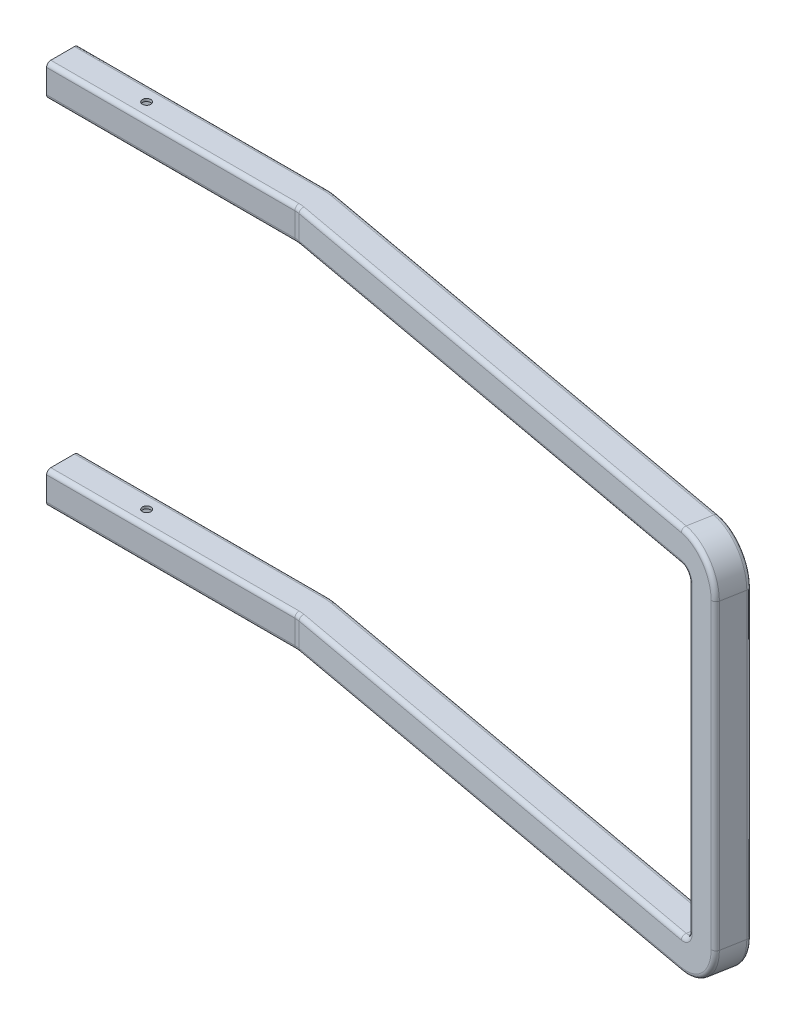
SolidWorks part; units mm, degrees
other "Markup1" [suppressed]
sketch "Sketch29" [suppressed] plane through (-50, 12.7, -12.7) normal (-0.6703, 0.7401, -0.0544) x (0.7356, 0.653, -0.1804)
sketch "Sketch30" [suppressed] plane through (-50, 20, -18.6944) normal (-0.6703, 0.7401, -0.0544) x (0.7356, 0.653, -0.1804)
sketch "Sketch34" [suppressed] plane through (-50, 20, -18.6944) normal (-0.6703, 0.7401, -0.0544) x (0.7356, 0.653, -0.1804)
sketch "Sketch35" [suppressed] plane through (-50, 30, -28.5496) normal (-0.6703, 0.7401, -0.0544) x (0.7356, 0.653, -0.1804)
sketch "Sketch36" [suppressed] plane through (-50, 30, -28.5496) normal (-0.6703, 0.7401, -0.0544) x (0.7356, 0.653, -0.1804)
sketch "Sketch37" plane through (-50, 30, -28.5496) normal (-0.6703, 0.7401, -0.0544) x (0.7356, 0.653, -0.1804)
sketch "Sketch38" plane through (-50, 25, -25) normal (-0.6703, 0.7401, -0.0544) x (0.7356, 0.653, -0.1804)
material "5052-O"
ref_plane "Front Plane" through (0, 0, 0) normal (0, 0, 1) x (1, 0, 0)
ref_plane "Top Plane" through (0, 0, 0) normal (0, 1, 0) x (1, 0, 0)
ref_plane "Right Plane" through (0, 0, 0) normal (1, 0, 0) x (0, 0, -1)
sketch "Sketch2" plane through (0, 0, 0) normal (1, 0, 0) x (0, 0, -1)
  line L1 (-14.05, -19.05) -> (14.05, -19.05)
  line L2 (-19.05, -14.05) -> (-19.05, 14.05)
  line L3 (-14.05, 19.05) -> (14.05, 19.05)
  line L4 (19.05, -14.05) -> (19.05, 14.05)
  line L5 (-19.05, -19.05) -> (19.05, 19.05) construction
  line L6 (-19.05, 19.05) -> (19.05, -19.05) construction
  arc A0 (19.05, -14.05) -> (14.05, -19.05) centre (14.05, -14.05) cw
  arc A1 (-14.05, -19.05) -> (-19.05, -14.05) centre (-14.05, -14.05) cw
  arc A2 (-19.05, 14.05) -> (-14.05, 19.05) centre (-14.05, 14.05) cw
  arc A3 (14.05, 19.05) -> (19.05, 14.05) centre (14.05, 14.05) cw
  point P0 (0, 0)
  dimension "D3" = 5
  dimension "D1" = 38.1
  dimension "D2" = 38.1
sketch3d "3DSketch2"
  line L0 (0, 0, 0) -> (840.2912, 0, 0) construction
  line L1 (840.2912, 0, 0) -> (840.2912, -210, 0) construction
  line L2 (840.2912, -210, 0) -> (840.2912, -210, 107.5) construction
  line L3 (0, 0, 0) -> (245.4843, 0, 0)
  line L4 (254.4426, 0, 0.8091) -> (810.7767, 0, 102.125)
  line L5 (0, 0, 0) -> (-50, 0, 0)
  line L6 (0, 0, 0) -> (0, -210, 0) construction
  line L7 (840.2912, -210, 107.5) -> (840.2912, -210, 287.5) construction
  line L8 (840.2912, -210, 287.5) -> (-9.7834, -210, 287.5) construction
  line L9 (840.2912, -30, 107.5) -> (840.2912, -210, 107.5)
  arc A0 (254.4426, 0, 0.8091) -> (245.4843, 0, 0) centre (245.4843, 0, 50) ccw
  arc A1 (840.2912, -30, 107.5) -> (810.7767, 0, 102.125) centre (810.7767, -30, 102.125) ccw
  point P16 (250, 0, 0)
  point P17 (245.4843, 50, 50)
  point P20 (840.2912, 0, 107.5)
  point P21 (805.4017, -30, 131.6396)
  dimension "5" = 50
  dimension "D9" = 30
  dimension "D1" = 250
  dimension "D2" = 50
  dimension "D3" = 210
  dimension "D4" = 107.5
  dimension "D5" = 210
  dimension "D6" = 600
  dimension "D7" = 180
  dimension "D8" = 210
sweep "Sweep-Thin3" add profiles "Sketch2" path "3DSketch2" parameters "D1"=3.175
sketch "Sketch21" plane through (0, 0, 0) normal (0, 1, 0) x (1, 0, 0)
  line L0 (0, 0) -> (245.4843, 0) construction
  circle A0 centre (50, 0) radius 5
  dimension "D1" = 10
  dimension "D2" = 50
extrude "Cut-Extrude3" cut sketch "Sketch21" against normal through all both and the other way through all
sketch "Sketch22" [suppressed] plane through (0, 0, 0) normal (0, 0, 1) x (1, 0, 0)
ref_plane "Plane1" [suppressed] through (0, -210, 0) normal (0, 1, 0) x (1, 0, 0)
ref_plane "Plane2" through (0, -210, 0) normal (0, -1, 0) x (-1, 0, 0)
ref_plane "Plane3" through (0, -210, 0) normal (0, -1, 0) x (-1, 0, 0)
mirror "Mirror1" about plane through (0, -210, 0) normal (0, -1, 0) of "Cut-Extrude3", "Sweep-Thin3"
ref_plane "Plane4" [suppressed] through (2.91, 0, -15.9792) normal (-0.1792, 0, 0.9838) x (0.9838, 0, 0.1792)
sketch "Sketch23" [suppressed] plane through (2.91, 0, -15.9792) normal (-0.1792, 0, 0.9838) x (0.9838, 0, 0.1792)
  line L0 (874.5043, -30) -> (874.5043, -390) construction
  line L1 (874.5043, 30) -> (674.5043, 30)
  line L2 (874.5043, 30) -> (874.5043, -450)
  line L3 (874.5043, -450) -> (674.5043, -450)
  line L4 (674.5043, 30) -> (674.5043, -450)
  line L5 (868.2597, -30) -> (868.2597, -390) construction
  point P8 (868.2597, -210)
  point P9 (874.5043, -210)
  dimension "D1" = 480
  dimension "D2" = 200
extrude "Boss-Extrude1" [suppressed] add sketch "Sketch23" along normal blind 25.4
sketch "Sketch25" [suppressed] plane through (2.91, 0, -15.9792) normal (0.1792, 0, -0.9838) x (-0.9838, 0, -0.1792)
  line L0 (-674.5043, -22.305) -> (-674.5043, -397.695) construction
  line L1 (-816.5543, -174.3) -> (-732.4543, -174.3) construction
  line L2 (-816.5543, -174.3) -> (-816.5543, -245.7) construction
  line L3 (-816.5543, -245.7) -> (-732.4543, -245.7) construction
  line L4 (-732.4543, -174.3) -> (-732.4543, -245.7) construction
  line L5 (-816.5543, -174.3) -> (-732.4543, -245.7) construction
  line L6 (-816.5543, -245.7) -> (-732.4543, -174.3) construction
  line L7 (-874.5043, 30) -> (-674.5043, 30) construction
  line L8 (-729.1662, -177.588) -> (-735.7423, -171.012) construction
  line L9 (-732.525, -180.9468) -> (-739.1011, -174.3707)
  line L10 (-725.8075, -174.2293) -> (-732.3836, -167.6532)
  line L11 (-732.4543, -210) -> (-816.5543, -210) construction
  line L12 (-774.5043, -174.3) -> (-774.5043, -245.7) construction
  line L13 (-729.1662, -242.412) -> (-735.7423, -248.988) construction
  line L14 (-732.525, -239.0532) -> (-739.1011, -245.6293)
  line L15 (-725.8075, -245.7707) -> (-732.3836, -252.3468)
  line L16 (-819.8423, -242.412) -> (-813.2662, -248.988) construction
  line L17 (-816.4836, -239.0532) -> (-809.9075, -245.6293)
  line L18 (-823.2011, -245.7707) -> (-816.625, -252.3468)
  line L19 (-819.8423, -177.588) -> (-813.2662, -171.012) construction
  line L20 (-816.4836, -180.9468) -> (-809.9075, -174.3707)
  line L21 (-823.2011, -174.2293) -> (-816.625, -167.6532)
  arc A0 (-732.525, -180.9468) -> (-725.8075, -174.2293) centre (-729.1662, -177.588) ccw
  arc A1 (-732.3836, -167.6532) -> (-739.1011, -174.3707) centre (-735.7423, -171.012) ccw
  arc A2 (-732.525, -239.0532) -> (-725.8075, -245.7707) centre (-729.1662, -242.412) cw
  arc A3 (-732.3836, -252.3468) -> (-739.1011, -245.6293) centre (-735.7423, -248.988) cw
  arc A4 (-816.4836, -239.0532) -> (-823.2011, -245.7707) centre (-819.8423, -242.412) ccw
  arc A5 (-816.625, -252.3468) -> (-809.9075, -245.6293) centre (-813.2662, -248.988) ccw
  arc A6 (-816.4836, -180.9468) -> (-823.2011, -174.2293) centre (-819.8423, -177.588) cw
  arc A7 (-816.625, -167.6532) -> (-809.9075, -174.3707) centre (-813.2662, -171.012) cw
  point P0 (-774.5043, -210)
  point P7 (-674.5043, -210)
  point P10 (-774.5043, 30)
  point P13 (-732.4543, -174.3)
  point P24 (-732.4543, -245.7)
  point P31 (-816.5543, -245.7)
  point P38 (-816.5543, -174.3)
  dimension "D1" = 71.4
  dimension "D2" = 84.1
  dimension "D3" = 45
  dimension "D4" = 9.5
  dimension "D5" = 9.3
extrude "Cut-Extrude4" [suppressed] cut sketch "Sketch25" against normal through all
ref_plane "Plane7" [suppressed] through (661.9492, 30, 129.8584) normal (0, -1, 0) x (-1, 0, 0)
sketch "Sketch28" [suppressed] plane through (-1.6408, 0, 9.0097) normal (-0.1792, 0, 0.9838) x (0.9838, 0, 0.1792)
  line L0 (874.5043, 30) -> (674.5043, 30) construction
  line L1 (717.3543, -159.2) -> (831.6543, -159.2)
  line L2 (717.3543, -159.2) -> (717.3543, -260.8)
  line L3 (717.3543, -260.8) -> (831.6543, -260.8)
  line L4 (831.6543, -159.2) -> (831.6543, -260.8)
  line L5 (717.3543, -159.2) -> (831.6543, -260.8) construction
  line L6 (717.3543, -260.8) -> (831.6543, -159.2) construction
  line L7 (674.5043, 30) -> (674.5043, -450) construction
  point P0 (774.5043, -210)
  point P7 (774.5043, 30)
  point P10 (674.5043, -210)
  dimension "D1" = 101.6
  dimension "D2" = 114.3
fillet "Fillet1" [suppressed] radius 30
fillet "Fillet2" [suppressed] radius 0.9144
ref_plane "Plane5" [suppressed] through (0, 0, 0) normal (-1, 0, 0) x (0, 0, 1)
ref_plane "EndOfTubePlane" [suppressed] through (140, 0, 0) normal (-1, 0, 0) x (0, 0, 1)
split line "Split Line1" [suppressed]
split line "Split Line2" [suppressed]
ref_plane "Plane8" [suppressed] through (806.7804, -391.4504, 124.0691) normal (0.9838, 0, 0.1792) x (0.1792, 0, -0.9838)
sketch "Sketch33" [suppressed] plane through (0, 0, 0) normal (0, 1, 0) x (1, 0, 0)
  line L0 (140, -28.5496) -> (245.4843, -28.5496) construction
  line L1 (249.3275, -28.8967) -> (665.6004, -104.7056) construction
  line L2 (-50, -28.5496) -> (140, -28.5496) construction
  arc A0 (140, -28.5496) -> (365.0664, -49.9743) centre (273.909, 185.2905) ccw
rib "Rib4" [suppressed] sketch "Sketch33" sketch "Sketch33" thickness 10 extrusion direction parallel to sketch draft on no parameters "D1"=10
chamfer "Chamfer1" [suppressed] distance 2.5 angle 45
mirror "Mirror2" [suppressed] about plane through (0, -210, 0) normal (0, -1, 0)
